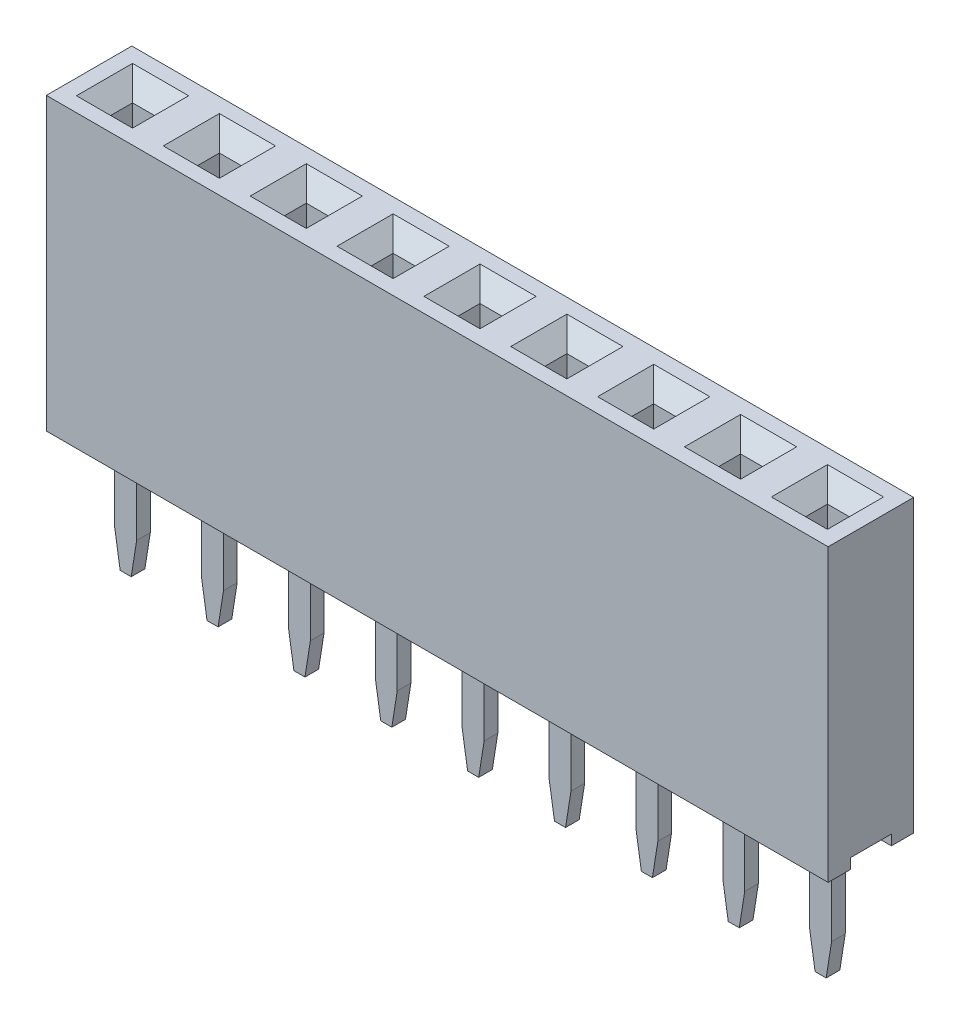
SolidWorks part; units mm, degrees
ref_plane "Front Plane" through (0, 0, 0) normal (0, 0, 1) x (1, 0, 0)
ref_plane "Top Plane" through (0, 0, 0) normal (0, 1, 0) x (1, 0, 0)
ref_plane "Right Plane" through (0, 0, 0) normal (1, 0, 0) x (0, 0, -1)
sketch "Sketch1" plane through (0, 0, 0) normal (0, 1, 0) x (1, 0, 0)
  line L1 (-1.27, -1.25) -> (1.27, -1.25)
  line L2 (-1.27, -1.25) -> (-1.27, 1.25)
  line L3 (-1.27, 1.25) -> (1.27, 1.25)
  line L4 (1.27, -1.25) -> (1.27, 1.25)
  line L5 (-1.27, -1.25) -> (1.27, 1.25) construction
  line L6 (-1.27, 1.25) -> (1.27, -1.25) construction
  point P0 (0, 0)
  dimension "D1" = 2.54
  dimension "D2" = 2.5
extrude "Boss-Extrude1" add sketch "Sketch1" along normal blind 8.5
sketch "Sketch2" plane through (0, 0, 0) normal (0, -1, 0) x (1, 0, 0)
  line L1 (1.27, 1.25) -> (1.27, -1.25) construction
  line L2 (-1.27, -0.6) -> (1.27, -0.6)
  line L3 (-1.27, -0.6) -> (-1.27, 0.6)
  line L4 (-1.27, 0.6) -> (1.27, 0.6)
  line L5 (1.27, -0.6) -> (1.27, 0.6)
  line L6 (-1.27, -0.6) -> (1.27, 0.6) construction
  line L7 (-1.27, 0.6) -> (1.27, -0.6) construction
  point P2 (0, 0)
  dimension "D1" = 1.2
extrude "Cut-Extrude1" cut sketch "Sketch2" against normal blind 0.3
sketch "Sketch3" plane through (0, 8.5, 0) normal (0, 1, 0) x (1, 0, 0)
  line L1 (-0.32, -0.32) -> (0.32, -0.32)
  line L2 (-0.32, -0.32) -> (-0.32, 0.32)
  line L3 (-0.32, 0.32) -> (0.32, 0.32)
  line L4 (0.32, -0.32) -> (0.32, 0.32)
  line L5 (-0.32, -0.32) -> (0.32, 0.32) construction
  line L6 (-0.32, 0.32) -> (0.32, -0.32) construction
  point P0 (0, 0)
  dimension "D1" = 0.64
  dimension "D2" = 0.64
extrude "Cut-Extrude2" cut sketch "Sketch3" against normal blind 6 and the other way through all
chamfer "Chamfer1" distance 0.5 angle 45 4 edges at (0, 8.5, -0.32) (-0.32, 8.5, 0) (0, 8.5, 0.32) (0.32, 8.5, 0)
sketch "Sketch4" plane through (0, 0.3, 0) normal (0, -1, 0) x (1, 0, 0)
  line L1 (-0.32, -0.2) -> (0.32, -0.2)
  line L2 (-0.32, -0.2) -> (-0.32, 0.2)
  line L3 (-0.32, 0.2) -> (0.32, 0.2)
  line L4 (0.32, -0.2) -> (0.32, 0.2)
  line L5 (-0.32, -0.2) -> (0.32, 0.2) construction
  line L6 (-0.32, 0.2) -> (0.32, -0.2) construction
  point P0 (0, 0)
  dimension "D1" = 0.4
  dimension "D2" = 0.64
extrude "Boss-Extrude2" add sketch "Sketch4" along normal blind 3.8
chamfer "Chamfer2" distance 1 angle 9 2 edges at (-0.32, -3.5, 0) (0.32, -3.5, 0)
pattern_linear "LPattern1" count 9 spacing 2.54 along (-1, 0, 0) of "Boss-Extrude1", "Cut-Extrude1", "Cut-Extrude2", "Chamfer1", "Boss-Extrude2", "Chamfer2"
